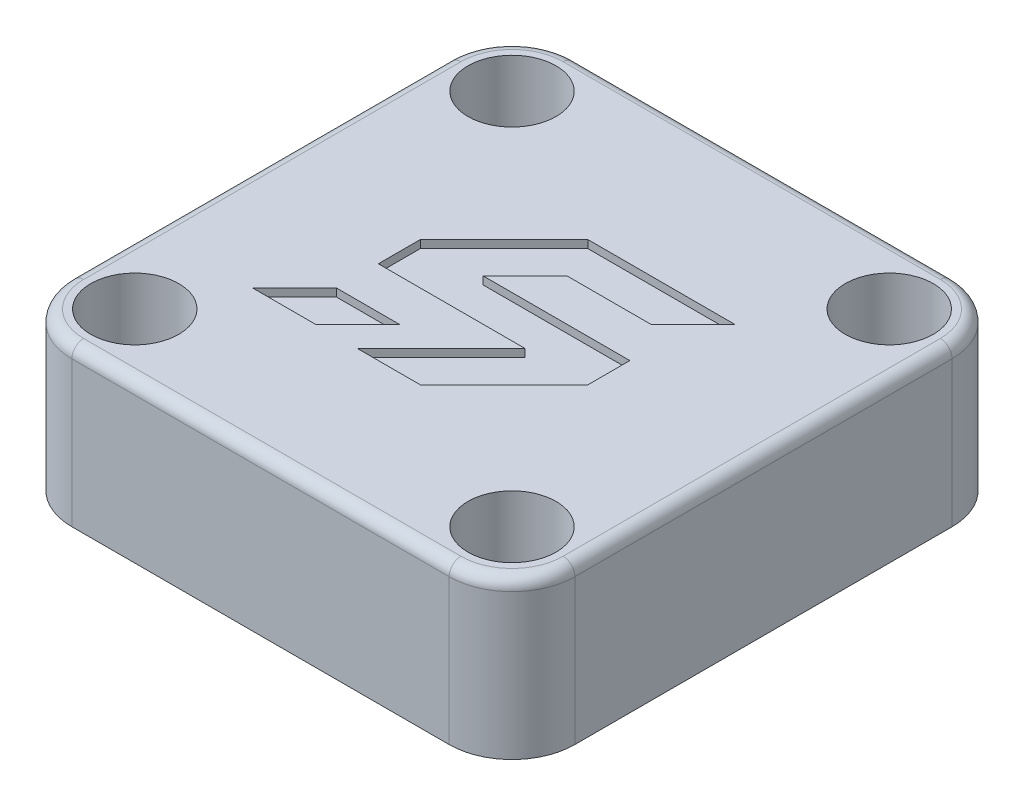
SolidWorks part; units mm, degrees
ref_plane "Front Plane" through (0, 0, 0) normal (0, 0, 1) x (1, 0, 0)
ref_plane "Top Plane" through (0, 0, 0) normal (0, 1, 0) x (1, 0, 0)
ref_plane "Right Plane" through (0, 0, 0) normal (1, 0, 0) x (0, 0, -1)
sketch "Sketch1" plane through (0, 0, 0) normal (0, 1, 0) x (1, 0, 0)
  line L0 (-16, 12) -> (-16, -12)
  line L1 (-12, 12) -> (12, 12)
  line L2 (-12, 12) -> (-12, -12)
  line L3 (-12, -12) -> (12, -12)
  line L4 (12, 12) -> (12, -12)
  line L5 (-12, 12) -> (12, -12) construction
  line L6 (-12, -12) -> (12, 12) construction
  line L7 (-12, -16) -> (12, -16)
  line L8 (16, 12) -> (16, -12)
  line L9 (-12, 16) -> (12, 16)
  circle A0 centre (-12, 12) radius 1.6
  circle A1 centre (12, 12) radius 1.6
  circle A2 centre (12, -12) radius 1.6
  circle A3 centre (-12, -12) radius 1.6
  circle A4 centre (-12, 12) radius 4
  circle A5 centre (12, 12) radius 4
  circle A6 centre (12, -12) radius 4
  circle A7 centre (-12, -12) radius 4
  point P0 (0, 0)
  dimension "D2" = 3.2
  dimension "D3" = 8
  dimension "D1" = 24
extrude "Boss-Extrude1" add sketch "Sketch1" along normal blind 10 contours A5 L9 A4 L1 | L1 A4 L2 A0 | A7 L2 A4 L0 | A7 L3 A3 L2 | A7 L7 A6 L3 | A6 L4 A2 L3 | A6 L8 A5 L4 | A7 L3 A6 L4 A5 L1 A4 L2 | L4 A6 L3 A2 | L3 A7 L2 A3 | L2 A4 L1 A0 | L4 A5 L1 A1 | L1 A5 L4 A1
sketch "Sketch2" plane through (0, 0, 0) normal (0, -1, 0) x (1, 0, 0)
  line L0 (-12, 16) -> (12, 16) construction
  line L1 (8, -16) -> (-8, -16)
  line L2 (8, -16) -> (8, 16)
  line L3 (8, 16) -> (-8, 16)
  line L4 (-8, -16) -> (-8, 16)
  line L5 (8, -16) -> (-8, 16) construction
  line L6 (8, 16) -> (-8, -16) construction
  circle A0 centre (0, 0) radius 14
  circle A3 centre (-12, 12) radius 1.6 construction
  circle A4 centre (-12, 12) radius 1.6
  line M12 (-12, -16) -> (12, -16)
  dimension "D1" = 28
  dimension "D2" = 4
extrude "Cut-Extrude1" cut sketch "Sketch2" against normal offset from surface (8.5 mm away) 1.5 contours A0 L4 L2 M12
sketch "Sketch3" plane through (0, 10, 0) normal (0, 1, 0) x (1, 0, 0)
  circle A0 centre (-12, 12) radius 2.8
  circle A1 centre (12, 12) radius 2.8
  circle A2 centre (12, -12) radius 2.8
  circle A3 centre (-12, -12) radius 2.8
  dimension "D1" = 5.6
extrude "Cut-Extrude2" cut sketch "Sketch3" against normal offset from surface (8 mm away) 2 up to face at (0, 0, -2.4574)
fillet "Fillet1" radius 3 2 edges at (8, 4.25, -11.4891) (-8, 4.25, -11.4891)
fillet "Fillet2" radius 3 5 edges at (8, 8.5, -14.4807) (-8, 8.5, -14.4807) (0, 8.5, 14) (-8.2775, 8.5, -11.7012) (8.2775, 8.5, -11.7012)
fillet "Fillet3" radius 0.75 8 edges at (0, 10, 16) (14.8284, 10, 14.8284) (16, 10, 0) (14.8284, 10, -14.8284) (0, 10, -16) (-14.8284, 10, -14.8284) (-16, 10, 0) (-14.8284, 10, 14.8284)
sketch "Sketch6" plane through (0, 10, 0) normal (0, 1, 0) x (1, 0, 0)
  line L0 (14.5917, 6.2385) -> (-1.4083, 6.2385)
  line L1 (14.5917, 6.2385) -> (1.2584, -7.0948)
  line L2 (11.9251, 3.5718) -> (-4.0749, 3.5718)
  line L3 (9.2584, 0.9052) -> (-6.7416, 0.9052)
  line L4 (6.5917, -1.7615) -> (-9.4083, -1.7615)
  line L5 (3.9251, -4.4282) -> (-12.0749, -4.4282)
  line L6 (1.2584, -7.0948) -> (-14.7416, -7.0948)
  line L7 (10.5917, 6.2385) -> (-2.7416, -7.0948)
  line L8 (6.5917, 6.2385) -> (-6.7416, -7.0948)
  line L9 (2.5917, 6.2385) -> (-10.7416, -7.0948)
  line L10 (-1.4083, 6.2385) -> (-14.7416, -7.0948)
  line L11 (-6.7416, 0.9052) -> (-6.7416, -1.7615)
  line L12 (6.5917, -1.7615) -> (6.5917, 0.9052)
  line L13 (-6.7416, -1.7615) -> (-6.7416, -4.4282) construction
  line L14 (-6.7416, -4.4282) -> (-9.4083, -7.0948)
  line L15 (-2.7416, -4.4282) -> (-5.4083, -7.0948)
  line L16 (-4.0749, -5.7615) -> (-8.0749, -5.7615) construction
  line L17 (-1.4083, -5.7615) -> (2.5917, -5.7615) construction
  line L18 (5.2584, 3.5718) -> (7.9251, 6.2385)
  dimension "D1" = 16
  dimension "D2" = 45
  dimension "D4" = 2.6667
  dimension "D3" = 6
  dimension "D5" = 5
extrude "Cut-Extrude3" cut sketch "Sketch6" against normal blind 0.5 contours L5 L14 L6 L8 | L15 L5 L8 L6 | L5 L7 L6 L1 | L4 L7 L5 L1 | L4 L12 L3 L7 | L3 L8 L4 L7 | L3 L9 L4 L8 | L3 L11 L4 L9 | L2 L10 L3 L9 | L0 L10 L2 L9 | L0 L9 L2 L8 | L2 L18 L0 L8
equation "\"D4@Sketch6\"=16/6"
